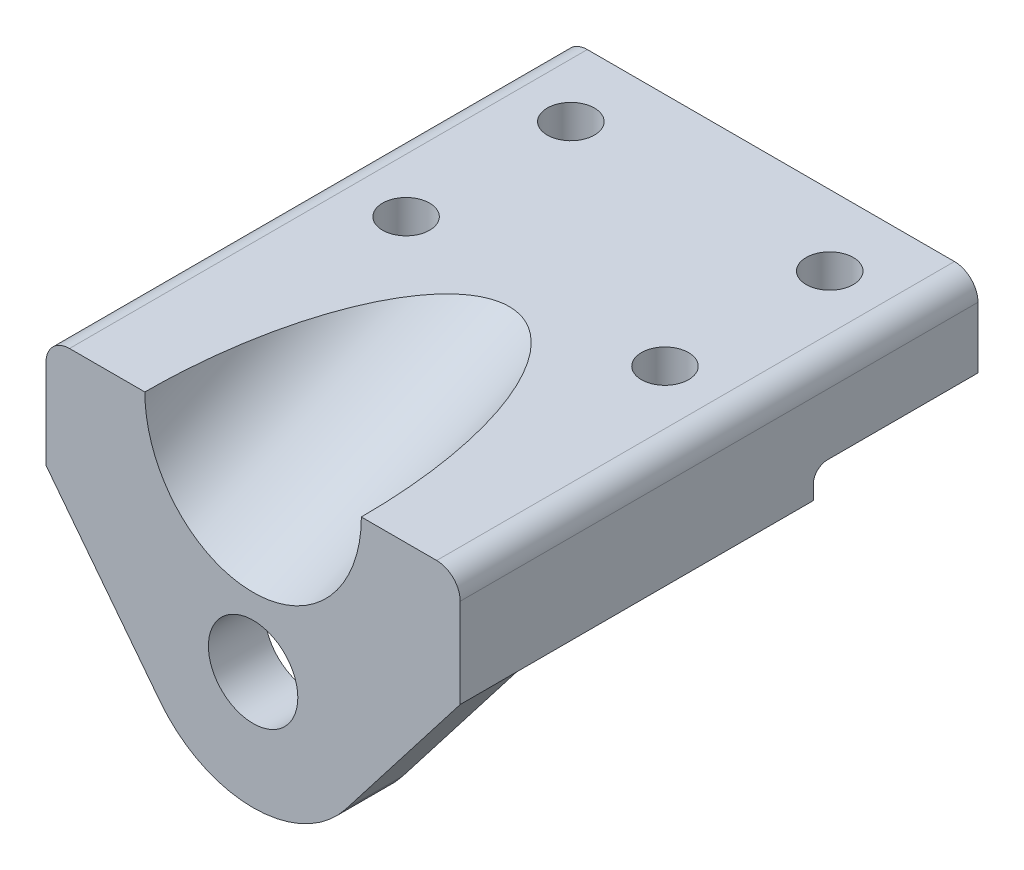
SolidWorks part; units mm, degrees
ref_plane "Front Plane" through (0, 0, 0) normal (0, 0, 1) x (1, 0, 0)
ref_plane "Top Plane" through (0, 0, 0) normal (0, 1, 0) x (1, 0, 0)
ref_plane "Right Plane" through (0, 0, 0) normal (1, 0, 0) x (0, 0, -1)
sketch "Sketch1" plane through (0, 0, 0) normal (0, 1, 0) x (1, 0, 0)
  line L1 (-44, 55) -> (44, 55)
  line L2 (-44, 55) -> (-44, -55)
  line L3 (-44, -55) -> (44, -55)
  line L4 (44, 55) -> (44, -55)
  line L5 (-44, 55) -> (44, -55) construction
  line L6 (-44, -55) -> (44, 55) construction
  point P0 (0, 0)
  dimension "D1" = 88
  dimension "D2" = 110
extrude "Boss-Extrude1" add sketch "Sketch1" along normal blind 18
sketch "Sketch2" plane through (0, 0, 0) normal (0, -1, 0) x (1, 0, 0)
  line L0 (44, 55) -> (44, -55) construction
  line L1 (-44, 55) -> (44, 55)
  line L2 (-44, 55) -> (-44, -20)
  line L3 (-44, -20) -> (44, -20)
  line L4 (44, 55) -> (44, -20)
  line L5 (44, -55) -> (-44, -55) construction
  dimension "D1" = 35
extrude "Boss-Extrude2" add sketch "Sketch2" along normal blind 6
sketch "Sketch3" plane through (0, 0, 55) normal (0, 0, 1) x (1, 0, 0)
  line L0 (-44, 18) -> (44, 18) construction
  line L1 (-44, -6) -> (-19.7692, -37.3029)
  line L2 (44, -6) -> (19.7692, -37.3029)
  line L3 (-44, -6) -> (44, -6)
  arc A1 (-19.7692, -37.3029) -> (19.7692, -37.3029) centre (0, -22) ccw
  circle A2 centre (0, -22) radius 9.5
  dimension "D1" = 50
  dimension "D2" = 19
  dimension "D3" = 40
extrude "Boss-Extrude3" add sketch "Sketch3" against normal blind 12
fillet "Fillet1" radius 3 1 edges at (0, 0, -20)
ref_plane "Plane1" through (0, 0, 0) normal (1, 0, 0) x (0, 0, -1)
sketch "Sketch4" plane through (0, 0, 0) normal (1, 0, 0) x (0, 0, -1)
  line L0 (-55, 18) -> (15.22, 50.7441) construction
  line L1 (-55, 18) -> (55, 18) construction
  line L2 (-55, -7.3777) -> (-0.5774, 18)
  line L3 (-55, 18) -> (-0.5774, 43.3777)
  line L4 (-45.2798, -2.8451) -> (24.9402, 29.8991) construction
  line L6 (-55, 18) -> (-55, -7.3777)
  line L7 (-55, -37.3029) -> (-55, -6) construction
  line L8 (-0.5774, 18) -> (-0.5774, 43.3777)
  point P5 (-0.5774, 18)
  dimension "D1" = 25
  dimension "D2" = 23
revolve "Cut-Revolve1" cut sketch "Sketch4" angle 360 about L3
fillet "Fillet2" radius 5 2 edges at (-44, 18, 0) (44, 18, 0)
sketch "Sketch5" plane through (0, 18, 0) normal (0, 1, 0) x (1, 0, 0)
  line L0 (0, 0) -> (0, 55) construction
  line L1 (39, 55) -> (-39, 55) construction
  line L2 (-27.5, 40) -> (-27.5, 5) construction
  line L3 (-27.5, 5) -> (0, 5) construction
  circle A0 centre (-27.5, 40) radius 5
  circle A1 centre (27.5, 40) radius 5
  circle A2 centre (27.5, 5) radius 5
  circle A3 centre (-27.5, 5) radius 5
  dimension "D4" = 10
  dimension "D1" = 35
  dimension "D2" = 15
  dimension "D3" = 27.5
  dimension "D5" = 2
  dimension "D6" = 2
extrude "Cut-Extrude1" cut sketch "Sketch5" against normal through all both and the other way through all
